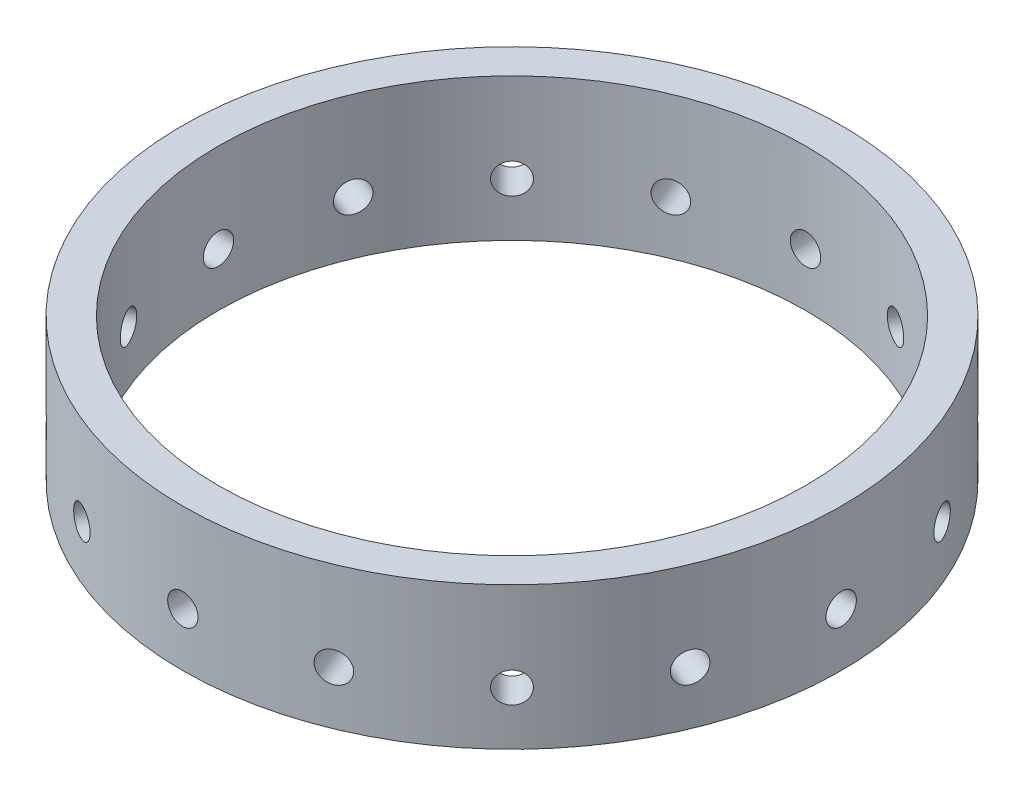
SolidWorks part; units mm, degrees
material "6061-T6 (SS)"
ref_plane "Front Plane" through (0, 0, 0) normal (0, 0, 1) x (1, 0, 0)
ref_plane "Top Plane" through (0, 0, 0) normal (0, 1, 0) x (1, 0, 0)
ref_plane "Right Plane" through (0, 0, 0) normal (1, 0, 0) x (0, 0, -1)
sketch "Sketch1" plane through (0, 0, 0) normal (0, 1, 0) x (1, 0, 0)
  circle A0 centre (0, 0) radius 58.7375
  circle A1 centre (0, 0) radius 52.3875
extrude "Boss-Extrude1" add sketch "Sketch1" along normal blind 25.4
ref_plane "Plane1" through (0, 0, -58.7375) normal (0, 0, -1) x (-1, 0, 0)
sketch "Sketch2" plane through (0, 0, -58.7375) normal (0, 0, -1) x (-1, 0, 0)
  line L0 (0, 0) -> (0, 9.525)
  point P4 (0, 9.525)
hole_wizard "Tap Drill for 1/4-28 Tap1" positions "Sketch3" profile "Sketch4" hole size "1/4-28" standard "ANSI Inch" end condition through all
sketch "Sketch3" plane through (0, 0, -58.7375) normal (0, 0, -1) x (-1, 0, 0)
  point P0 (0, 9.525)
sketch "Sketch4" plane through (0, 9.525, -58.7375) normal (1, 0, 0) x (0, 1, 0)
  line L0 (0, 0) -> (0, 117.475)
  line L1 (0, 117.475) -> (2.7051, 117.475)
  line L2 (2.7051, 117.475) -> (2.7051, 0)
  line L5 (2.7051, 0) -> (0, 0)
  line L11 (0, -6.35) -> (0, 107.95) construction
  dimension "Thru Hole Dia." = 5.4102
  dimension "Thru Hole Depth" = 117.475
sketch "Sketch5" plane through (0, 0, 0) normal (0, 0, 1) x (1, 0, 0)
  line L0 (0, 0) -> (0, 24.4952)
pattern_circular "CirPattern1" count 16 over 360 about axis through (0, 0, 0) along (0, 1, 0) of "Tap Drill for 1/4-28 Tap1"
ref_plane "Plane2" through (0, 9.525, 0) normal (0, 1, 0) x (1, 0, 0)
